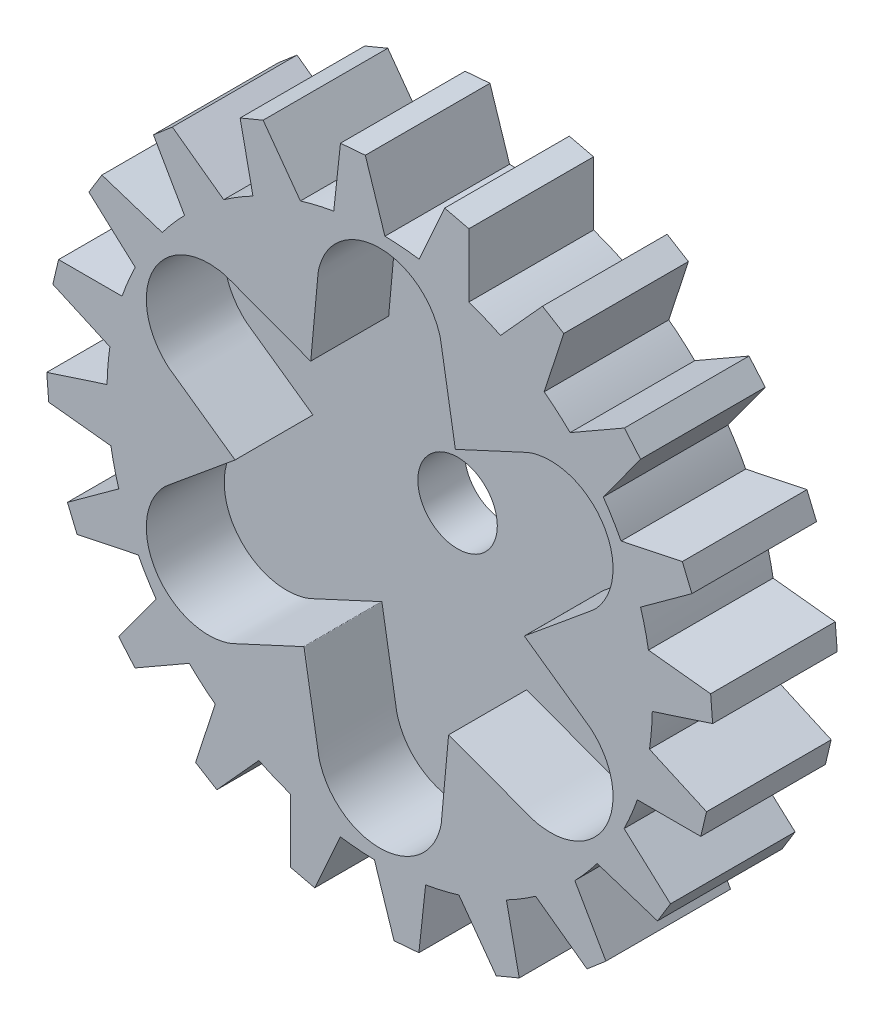
SolidWorks part; units mm, degrees
ref_plane "Front Plane" through (0, 0, 0) normal (0, 0, 1) x (1, 0, 0)
ref_plane "Top Plane" through (0, 0, 0) normal (0, 1, 0) x (1, 0, 0)
ref_plane "Right Plane" through (0, 0, 0) normal (1, 0, 0) x (0, 0, -1)
sketch "Sketch1" plane through (0, 0, 0) normal (0, 0, 1) x (1, 0, 0)
  line L4 (4.1704, 20.9787) -> (2.5269, 17.3166)
  line L5 (4.1704, 20.9787) -> (5.7269, 20.6083)
  line L6 (5.7269, 20.6083) -> (5.7269, 16.5364)
  line L11 (10.449, 18.6632) -> (7.7544, 15.6882)
  line L12 (10.449, 18.6632) -> (11.8149, 17.8299)
  line L13 (11.8149, 17.8299) -> (10.5566, 13.9573)
  line L14 (15.7049, 14.5208) -> (12.2228, 12.5241)
  line L15 (15.7049, 14.5208) -> (16.7464, 13.3063)
  line L16 (16.7464, 13.3063) -> (14.353, 10.012)
  line L17 (19.4234, 8.9571) -> (15.4947, 8.1341)
  line L18 (19.4234, 8.9571) -> (20.0386, 7.4801)
  line L19 (20.0386, 7.4801) -> (16.7444, 5.0867)
  line L20 (21.2407, 2.5165) -> (17.2499, 2.9479)
  line L21 (21.2407, 2.5165) -> (21.3693, 0.9217)
  line L22 (21.3693, 0.9217) -> (17.4968, -0.3366)
  line L23 (20.9787, -4.1704) -> (17.3166, -2.5269)
  line L24 (20.9787, -4.1704) -> (20.6083, -5.7269)
  line L25 (20.6083, -5.7269) -> (16.5364, -5.7269)
  line L26 (18.6632, -10.449) -> (15.6882, -7.7544)
  line L27 (18.6632, -10.449) -> (17.8299, -11.8149)
  line L28 (17.8299, -11.8149) -> (13.9573, -10.5566)
  line L29 (14.5208, -15.7049) -> (12.5241, -12.2228)
  line L30 (14.5208, -15.7049) -> (13.3063, -16.7464)
  line L31 (13.3063, -16.7464) -> (10.012, -14.353)
  line L32 (8.9571, -19.4234) -> (8.1341, -15.4947)
  line L33 (8.9571, -19.4234) -> (7.4801, -20.0386)
  line L34 (7.4801, -20.0386) -> (5.0867, -16.7444)
  line L35 (2.5165, -21.2407) -> (2.9479, -17.2499)
  line L36 (2.5165, -21.2407) -> (0.9217, -21.3693)
  line L37 (0.9217, -21.3693) -> (-0.3366, -17.4968)
  line L38 (-4.1704, -20.9787) -> (-2.5269, -17.3166)
  line L39 (-4.1704, -20.9787) -> (-5.7269, -20.6083)
  line L40 (-5.7269, -20.6083) -> (-5.7269, -16.5364)
  line L41 (-10.449, -18.6632) -> (-7.7544, -15.6882)
  line L42 (-10.449, -18.6632) -> (-11.8149, -17.8299)
  line L43 (-11.8149, -17.8299) -> (-10.5566, -13.9573)
  line L44 (-15.7049, -14.5208) -> (-12.2228, -12.5241)
  line L45 (-15.7049, -14.5208) -> (-16.7464, -13.3063)
  line L46 (-16.7464, -13.3063) -> (-14.353, -10.012)
  line L47 (-19.4234, -8.9571) -> (-15.4947, -8.1341)
  line L48 (-19.4234, -8.9571) -> (-20.0386, -7.4801)
  line L49 (-20.0386, -7.4801) -> (-16.7444, -5.0867)
  line L50 (-21.2407, -2.5165) -> (-17.2499, -2.9479)
  line L51 (-21.2407, -2.5165) -> (-21.3693, -0.9217)
  line L52 (-21.3693, -0.9217) -> (-17.4968, 0.3366)
  line L53 (-20.9787, 4.1704) -> (-17.3166, 2.5269)
  line L54 (-20.9787, 4.1704) -> (-20.6083, 5.7269)
  line L55 (-20.6083, 5.7269) -> (-16.5364, 5.7269)
  line L56 (-18.6632, 10.449) -> (-15.6882, 7.7544)
  line L57 (-18.6632, 10.449) -> (-17.8299, 11.8149)
  line L58 (-17.8299, 11.8149) -> (-13.9573, 10.5566)
  line L59 (-14.5208, 15.7049) -> (-12.5241, 12.2228)
  line L60 (-14.5208, 15.7049) -> (-13.3063, 16.7464)
  line L61 (-13.3063, 16.7464) -> (-10.012, 14.353)
  line L62 (-8.9571, 19.4234) -> (-8.1341, 15.4947)
  line L63 (-8.9571, 19.4234) -> (-7.4801, 20.0386)
  line L64 (-7.4801, 20.0386) -> (-5.0867, 16.7444)
  line L65 (-2.5165, 21.2407) -> (-2.9479, 17.2499)
  line L66 (-2.5165, 21.2407) -> (-0.9217, 21.3693)
  line L67 (-0.9217, 21.3693) -> (0.3366, 17.4968)
  circle A2 centre (0, 0) radius 21.3892 construction
  circle A3 centre (0, 0) radius 17.5
  point P0 (0, 0)
  point P94 (0, 0)
  dimension "D5" = 20
  dimension "D1" = 35
  dimension "D3" = 1.6
  dimension "D4" = 3.2
extrude "Boss-Extrude1" add sketch "Sketch1" along normal blind 8 contours A3 L6 L5 L4 | A3 L13 L12 L11 | A3 L16 L15 L14 | A3 L19 L18 L17 | A3 L22 L21 L20 | A3 L25 L24 L23 | A3 L28 L27 L26 | A3 L31 L30 L29 | A3 L34 L33 L32 | A3 L37 L36 L35 | A3 L40 L39 L38 | A3 L43 L42 L41 | A3 L46 L45 L44 | A3 L49 L48 L47 | A3 L52 L51 L50 | A3 L55 L54 L53 | A3 L58 L57 L56 | A3 L61 L60 L59 | A3 L64 L63 L62 | A3 L67 L66 L65 | A3
sketch "Sketch3" plane through (0, 0, 8) normal (0, 0, 1) x (1, 0, 0)
  circle A0 centre (0, 0) radius 2.55
  dimension "D1" = 5.1
extrude "Cut-Extrude1" cut sketch "Sketch3" against normal through all both and the other way through all
sketch "Sketch4" plane through (0, 0, 8) normal (0, 0, 1) x (1, 0, 0)
  line L0 (-26.1715, 0) -> (-6.1185, 0) construction
  line L1 (0, -22.4973) -> (0, 10.9324) construction
  line L2 (-3.5449, 6.7684) -> (-2.9879, 12.9457) construction
  line L3 (2.9584, 13.1741) -> (4.0891, 6.4542) construction
  line L4 (4.0891, 6.4542) -> (9.7174, 9.0604) construction
  line L5 (12.8883, 4.025) -> (7.6341, -0.3142) construction
  line L6 (7.6341, -0.3142) -> (12.7053, -3.8853) construction
  line L7 (9.9299, -9.1491) -> (3.5449, -6.7684) construction
  line L8 (3.5449, -6.7684) -> (2.9879, -12.9457) construction
  line L9 (-2.9584, -13.1741) -> (-4.0891, -6.4542) construction
  line L10 (-4.0891, -6.4542) -> (-9.7174, -9.0604) construction
  line L11 (-12.8883, -4.025) -> (-7.6341, 0.3142) construction
  line L12 (-7.6341, 0.3142) -> (-12.7053, 3.8853) construction
  line L13 (-9.9299, 9.1491) -> (-3.5449, 6.7684) construction
  line L14 (-5, 0) -> (28.8218, 0) construction
  line L15 (-9.5805, 10.0861) -> (-4.4232, 8.1631) construction
  line L16 (-4.4232, 8.1631) -> (-3.9838, 13.0355) construction
  line L17 (3.9446, 13.34) -> (4.8578, 7.9122) construction
  line L18 (4.8578, 7.9122) -> (9.2972, 9.9679) construction
  line L19 (13.5251, 3.2539) -> (9.2811, -0.2509) construction
  line L20 (9.2811, -0.2509) -> (13.281, -3.0677) construction
  line L21 (9.5805, -10.0861) -> (4.4232, -8.1631) construction
  line L22 (4.4232, -8.1631) -> (3.9838, -13.0355) construction
  line L23 (-3.9446, -13.34) -> (-4.8578, -7.9122) construction
  line L24 (-4.8578, -7.9122) -> (-9.2972, -9.9679) construction
  line L25 (-13.5251, -3.2539) -> (-9.2811, 0.2509) construction
  line L26 (-9.2811, 0.2509) -> (-13.281, 3.0677) construction
  arc A1 (-2.9879, 12.9457) -> (2.9584, 13.1741) centre (0, 12.6763) cw construction
  arc A2 (9.7174, 9.0604) -> (12.8883, 4.025) centre (10.978, 6.3381) cw construction
  arc A3 (12.7053, -3.8853) -> (9.9299, -9.1491) centre (10.978, -6.3381) cw construction
  arc A4 (2.9879, -12.9457) -> (-2.9584, -13.1741) centre (0, -12.6763) cw construction
  arc A5 (-9.7174, -9.0604) -> (-12.8883, -4.025) centre (-10.978, -6.3381) cw construction
  arc A6 (-12.7053, 3.8853) -> (-9.9299, 9.1491) centre (-10.978, 6.3381) cw construction
  arc A7 (-3.9838, 13.0355) -> (3.9446, 13.34) centre (0, 12.6763) cw construction
  arc A8 (9.2972, 9.9679) -> (13.5251, 3.2539) centre (10.978, 6.3381) cw construction
  arc A9 (13.281, -3.0677) -> (9.5805, -10.0861) centre (10.978, -6.3381) cw construction
  arc A10 (3.9838, -13.0355) -> (-3.9446, -13.34) centre (0, -12.6763) cw construction
  arc A11 (-9.2972, -9.9679) -> (-13.5251, -3.2539) centre (-10.978, -6.3381) cw construction
  arc A12 (-13.281, 3.0677) -> (-9.5805, 10.0861) centre (-10.978, 6.3381) cw construction
  spline S0 degree 3 poles (8.4215, -9.6539) (7.0952, -9.1594) (5.769, -8.6649) (4.4428, -8.1704) (4.4403, -8.1695) (4.4353, -8.1676) (4.4223, -8.1736) (4.4218, -8.179) (4.4216, -8.1816) (4.3123, -9.3936) (4.203, -10.6055) (4.0937, -11.8174) (4.0815, -11.9528) (4.0571, -12.2235) (4.0204, -12.6295) (3.996, -12.9002) (3.9838, -13.0355) (3.9714, -13.1733) (3.9466, -13.4488) (3.8298, -13.8555) (3.7346, -14.1156) (3.6805, -14.2429) (2.1554, -17.8257) (-1.7353, -17.982) (-3.5429, -14.5332) (-3.6078, -14.4093) (-3.7247, -14.1547) (-3.8749, -13.7538) (-3.9213, -13.4779) (-3.9446, -13.34) (-3.9674, -13.2045) (-4.013, -12.9334) (-4.0814, -12.5268) (-4.127, -12.2557) (-4.1498, -12.1202) (-4.3847, -10.7244) (-4.6195, -9.3286) (-4.8544, -7.9328) (-4.8548, -7.9302) (-4.8557, -7.9249) (-4.8674, -7.9166) (-4.8723, -7.9189) (-4.8747, -7.92) (-5.9789, -8.4313) (-7.0831, -8.9426) (-8.1874, -9.4539) (-8.3107, -9.511) (-8.5573, -9.6253) (-8.9272, -9.7966) (-9.1739, -9.9108) (-9.2972, -9.9679) (-9.4227, -10.026) (-9.6737, -10.1422) (-10.0843, -10.2444) (-10.3572, -10.2921) (-10.4945, -10.3088) (-14.3598, -10.7795) (-16.4405, -7.4882) (-14.3575, -4.1984) (-14.2827, -4.0802) (-14.1206, -3.8516) (-13.8486, -3.5211) (-13.6329, -3.343) (-13.5251, -3.2539) (-13.4191, -3.1664) (-13.2071, -2.9914) (-12.8892, -2.7288) (-12.6772, -2.5538) (-12.5713, -2.4662) (-11.4799, -1.565) (-10.3886, -0.6637) (-9.2972, 0.2376) (-9.2951, 0.2393) (-9.291, 0.2427) (-9.2897, 0.257) (-9.2941, 0.2601) (-9.2963, 0.2616) (-10.2912, 0.9622) (-11.2861, 1.6629) (-12.281, 2.3635) (-12.3921, 2.4417) (-12.6144, 2.5982) (-12.9477, 2.8329) (-13.1699, 2.9894) (-13.281, 3.0677) (-13.3941, 3.1473) (-13.6203, 3.3066) (-13.9141, 3.611) (-14.0918, 3.8235) (-14.1749, 3.9341) (-16.5152, 7.0462) (-14.7052, 10.4938) (-10.8146, 10.3348) (-10.6749, 10.3291) (-10.3959, 10.303) (-9.9737, 10.2327) (-9.7116, 10.135) (-9.5805, 10.0861) (-9.4517, 10.0381) (-9.1942, 9.942) (-8.8078, 9.798) (-8.5502, 9.7019) (-8.4215, 9.6539) (-7.0952, 9.1594) (-5.769, 8.6649) (-4.4428, 8.1704) (-4.4403, 8.1695) (-4.4353, 8.1676) (-4.4223, 8.1736) (-4.4218, 8.179) (-4.4216, 8.1816) (-4.3123, 9.3936) (-4.203, 10.6055) (-4.0937, 11.8174) (-4.0815, 11.9528) (-4.0571, 12.2235) (-4.0204, 12.6295) (-3.996, 12.9002) (-3.9838, 13.0355) (-3.9714, 13.1733) (-3.9466, 13.4488) (-3.8298, 13.8555) (-3.7346, 14.1156) (-3.6805, 14.2429) (-2.1554, 17.8257) (1.7353, 17.982) (3.5429, 14.5332) (3.6078, 14.4093) (3.7247, 14.1547) (3.8749, 13.7538) (3.9213, 13.4779) (3.9446, 13.34) (3.9674, 13.2045) (4.013, 12.9334) (4.0814, 12.5268) (4.127, 12.2557) (4.1498, 12.1202) (4.3847, 10.7244) (4.6195, 9.3286) (4.8544, 7.9328) (4.8548, 7.9302) (4.8557, 7.9249) (4.8674, 7.9166) (4.8723, 7.9189) (4.8747, 7.92) (5.9789, 8.4313) (7.0831, 8.9426) (8.1874, 9.4539) (8.3107, 9.511) (8.5573, 9.6253) (8.9272, 9.7966) (9.1739, 9.9108) (9.2972, 9.9679) (9.4227, 10.026) (9.6737, 10.1422) (10.0843, 10.2444) (10.3572, 10.2921) (10.4945, 10.3088) (14.3598, 10.7795) (16.4405, 7.4882) (14.3575, 4.1984) (14.2827, 4.0802) (14.1206, 3.8516) (13.8486, 3.5211) (13.6329, 3.343) (13.5251, 3.2539) (13.4191, 3.1664) (13.2071, 2.9914) (12.8892, 2.7288) (12.6772, 2.5538) (12.5713, 2.4662) (11.4799, 1.565) (10.3886, 0.6637) (9.2972, -0.2376) (9.2951, -0.2393) (9.291, -0.2427) (9.2897, -0.257) (9.2941, -0.2601) (9.2963, -0.2616) (10.2912, -0.9622) (11.2861, -1.6629) (12.281, -2.3635) (12.3921, -2.4417) (12.6144, -2.5982) (12.9477, -2.8329) (13.1699, -2.9894) (13.281, -3.0677) (13.3941, -3.1473) (13.6203, -3.3066) (13.9141, -3.611) (14.0918, -3.8235) (14.1749, -3.9341) (16.5152, -7.0462) (14.7052, -10.4938) (10.8146, -10.3348) (10.6749, -10.3291) (10.3959, -10.303) (9.9737, -10.2327) (9.7116, -10.135) (9.5805, -10.0861) (9.4517, -10.0381) (9.1942, -9.942) (8.8078, -9.798) (8.5502, -9.7019) (8.4215, -9.6539) (7.0952, -9.1594) (5.769, -8.6649) knots -0.003417 0 0 0 0.035185 0.035185 0.035185 0.035251 0.035318 0.035384 0.035384 0.035384 0.065633 0.065633 0.065633 0.069011 0.072389 0.075768 0.075768 0.075768 0.079206 0.082644 0.086083 0.086083 0.086083 0.145985 0.145985 0.145985 0.149462 0.152939 0.156417 0.156417 0.156417 0.159833 0.16325 0.166667 0.166667 0.166667 0.201852 0.201852 0.201852 0.201918 0.201984 0.202051 0.202051 0.202051 0.2323 0.2323 0.2323 0.235678 0.239056 0.242434 0.242434 0.242434 0.245873 0.249311 0.25275 0.25275 0.25275 0.312652 0.312652 0.312652 0.316129 0.319606 0.323083 0.323083 0.323083 0.3265 0.329917 0.333333 0.333333 0.333333 0.368518 0.368518 0.368518 0.368585 0.368651 0.368717 0.368717 0.368717 0.398967 0.398967 0.398967 0.402345 0.405723 0.409101 0.409101 0.409101 0.412539 0.415978 0.419416 0.419416 0.419416 0.479318 0.479318 0.479318 0.482796 0.486273 0.48975 0.48975 0.48975 0.493167 0.496583 0.5 0.5 0.5 0.535185 0.535185 0.535185 0.535251 0.535318 0.535384 0.535384 0.535384 0.565633 0.565633 0.565633 0.569011 0.572389 0.575768 0.575768 0.575768 0.579206 0.582644 0.586083 0.586083 0.586083 0.645985 0.645985 0.645985 0.649462 0.652939 0.656417 0.656417 0.656417 0.659833 0.66325 0.666667 0.666667 0.666667 0.701852 0.701852 0.701852 0.701918 0.701984 0.702051 0.702051 0.702051 0.7323 0.7323 0.7323 0.735678 0.739056 0.742434 0.742434 0.742434 0.745873 0.749311 0.75275 0.75275 0.75275 0.812652 0.812652 0.812652 0.816129 0.819606 0.823083 0.823083 0.823083 0.8265 0.829917 0.833333 0.833333 0.833333 0.868518 0.868518 0.868518 0.868585 0.868651 0.868717 0.868717 0.868717 0.898967 0.898967 0.898967 0.902345 0.905723 0.909101 0.909101 0.909101 0.912539 0.915978 0.919416 0.919416 0.919416 0.979318 0.979318 0.979318 0.982796 0.986273 0.98975 0.98975 0.98975 0.993167 0.996583 1 1 1 1.035185 1.035185 1.035185 weights 1 1 1 1 1 1 1 1 1 1 1 1 1 1 1 1 1 1 1 1 1 1 0.618855 0.618855 1 1 1 1 1 1 1 1 1 1 1 1 1 1 1 1 1 1 1 1 1 1 1 1 1 1 1 1 1 1 1 1 0.618855 0.618855 1 1 1 1 1 1 1 1 1 1 1 1 1 1 1 1 1 1 1 1 1 1 1 1 1 1 1 1 1 1 1 1 0.618855 0.618855 1 1 1 1 1 1 1 1 1 1 1 1 1 1 1 1 1 1 1 1 1 1 1 1 1 1 1 1 1 1 1 1 0.618855 0.618855 1 1 1 1 1 1 1 1 1 1 1 1 1 1 1 1 1 1 1 1 1 1 1 1 1 1 1 1 1 1 1 1 0.618855 0.618855 1 1 1 1 1 1 1 1 1 1 1 1 1 1 1 1 1 1 1 1 1 1 1 1 1 1 1 1 1 1 1 1 0.618855 0.618855 1 1 1 1 1 1 1 1 1 1 1 1 1 only from (8.4215, -9.6539) to (8.4215, -9.6539)
  point P11 (-0.1151, 15.6741)
  point P40 (0, 0)
  dimension "D1" = 1
  dimension "D2" = 3
  dimension "D3" = 2.5
  dimension "D5" = 6
extrude "Cut-Extrude2" cut sketch "Sketch4" against normal blind 5
